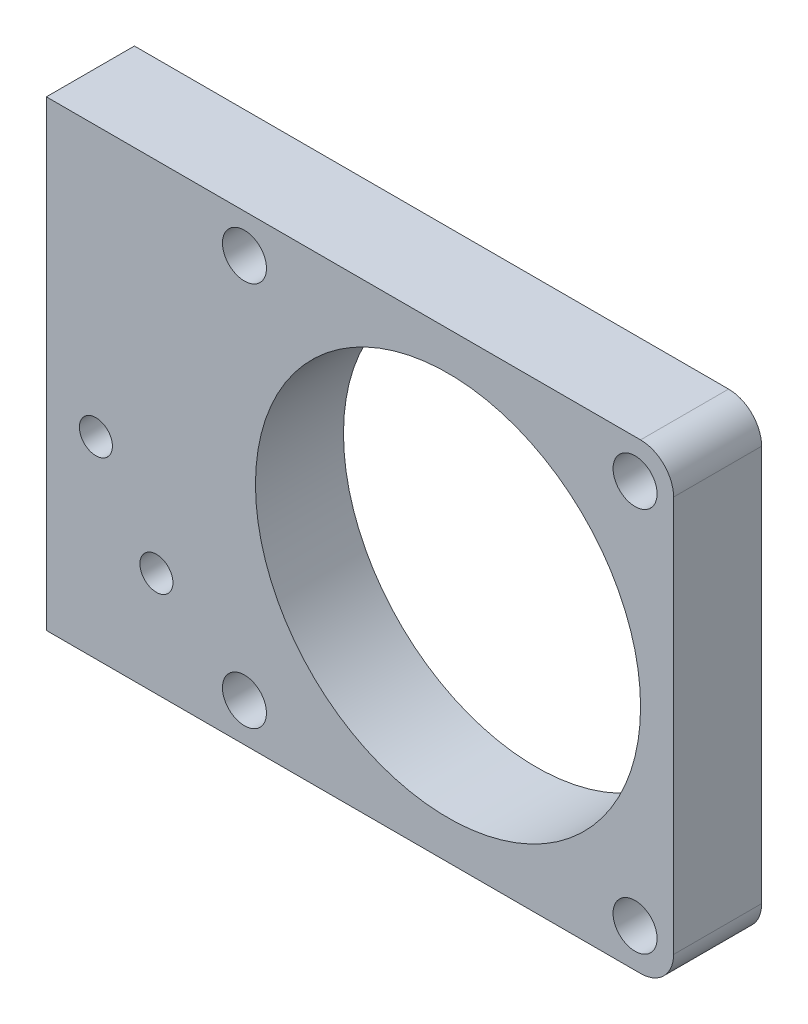
SolidWorks part; units mm, degrees
ref_plane "Front Plane" through (0, 0, 0) normal (0, 0, 1) x (1, 0, 0)
ref_plane "Top Plane" through (0, 0, 0) normal (0, 1, 0) x (1, 0, 0)
ref_plane "Right Plane" through (0, 0, 0) normal (1, 0, 0) x (0, 0, -1)
sketch "Sketch1" plane through (0, 0, 0) normal (0, 0, 1) x (1, 0, 0)
  line L1 (-28.5, -21) -> (28.5, -21)
  line L2 (-28.5, -21) -> (-28.5, 21)
  line L3 (-28.5, 21) -> (28.5, 21)
  line L4 (28.5, -21) -> (28.5, 21)
  line L5 (-28.5, -21) -> (28.5, 21) construction
  line L6 (-28.5, 21) -> (28.5, -21) construction
  point P0 (0, 0)
  point P6 (28.5, 0)
  dimension "D1" = 57
  dimension "D2" = 42
extrude "Boss-Extrude1" add sketch "Sketch1" along normal blind 8
sketch "Sketch2" plane through (0, 0, 8) normal (0, 0, 1) x (1, 0, 0)
  line L0 (28.5, -21) -> (28.5, 21) construction
  line L1 (28.5, 21) -> (-28.5, 21) construction
  line L2 (-28.5, -21) -> (28.5, -21) construction
  line L5 (-28.5, 21) -> (-28.5, -21) construction
  circle A0 centre (8, 0) radius 17.5
  circle A1 centre (25, 17.5) radius 2
  circle A2 centre (-10.5, 17.5) radius 2
  circle A3 centre (25, -17.5) radius 2
  circle A4 centre (-10.5, -17.5) radius 2
  circle A5 centre (-18.5, -11.5) radius 1.5
  circle A6 centre (-24, -3.5) radius 1.5
  point P0 (28.5, 0)
  point P22 (0, 0)
  point P24 (-28.5, -0.255)
  point P25 (-28.5, -5.3898)
  dimension "D1" = 35
  dimension "D3" = 4
  dimension "D7" = 3
  dimension "D8" = 3
  dimension "D2" = 20.5
  dimension "D4" = 3.5
  dimension "D5" = 3.5
  dimension "D9" = 9.5
  dimension "D10" = 17.5
  dimension "D11" = 4.5
  dimension "D12" = 10
  dimension "D6" = 2
extrude "Cut-Extrude1" cut sketch "Sketch2" against normal through all
fillet "Fillet1" radius 3 1 edges at (28.5, -21, 4)
fillet "Fillet2" radius 3 1 edges at (28.5, 21, 4)
sketch "Sketch3" plane through (-28.5, 0, 0) normal (-1, 0, 0) x (0, 0, 1)
  line L0 (4, 21) -> (4, -21) construction
  line L1 (8, 21) -> (0, 21) construction
  line L2 (8, -21) -> (0, -21) construction
  line L3 (0, 0) -> (8, 0) construction
  line L4 (8, 21) -> (8, -21) construction
  circle A0 centre (4, 16) radius 2
  circle A1 centre (4, -16) radius 2
  dimension "D1" = 4
  dimension "D2" = 5
extrude "Cut-Extrude2" cut sketch "Sketch3" against normal blind 13
